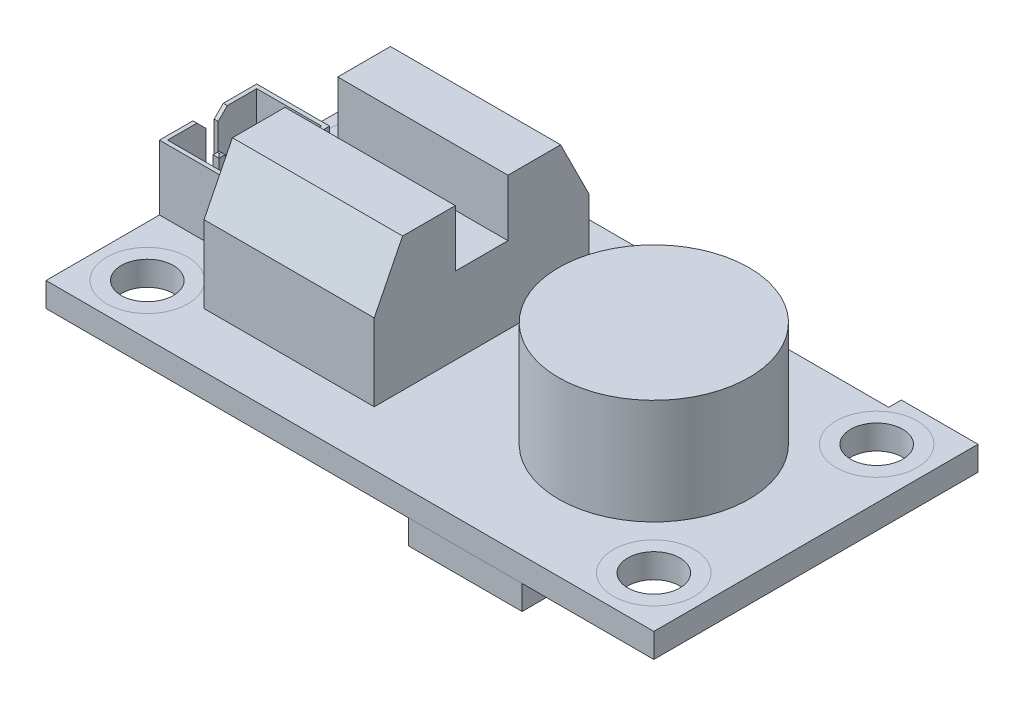
SolidWorks part; units mm, degrees
material "A-Glass Fiber"
ref_plane "Front Plane" through (0, 0, 0) normal (0, 0, 1) x (1, 0, 0)
ref_plane "Top Plane" through (0, 0, 0) normal (0, 1, 0) x (1, 0, 0)
ref_plane "Right Plane" through (0, 0, 0) normal (1, 0, 0) x (0, 0, -1)
sketch "Sketch1" plane through (0, 0, 0) normal (0, 1, 0) x (1, 0, 0)
  line L1 (19.05, -10.16) -> (-19.05, -10.16)
  line L2 (19.05, -10.16) -> (19.05, 10.16)
  line L3 (19.05, 10.16) -> (-19.05, 10.16)
  line L4 (-19.05, -10.16) -> (-19.05, 10.16)
  line L5 (19.05, -10.16) -> (-19.05, 10.16) construction
  line L6 (19.05, 10.16) -> (-19.05, -10.16) construction
  point P0 (0, 0)
  dimension "D1" = 38.1
  dimension "D2" = 20.32
extrude "Boss-Extrude1" add sketch "Sketch1" along normal blind 1.524
hole_wizard "#4 Clearance Hole1" positions "Sketch2" profile "Sketch3" hole size "#4" standard "ANSI Inch" end condition through all
sketch "Sketch2" plane through (0, 1.524, 0) normal (0, 1, 0) x (1, 0, 0)
  line L9 (-15.875, 6.985) -> (15.875, 6.985)
  line L10 (-15.875, 6.985) -> (-15.875, -6.985)
  line L11 (-15.875, -6.985) -> (15.875, -6.985)
  line L12 (15.875, 6.985) -> (15.875, -6.985)
  line L13 (19.05, -10.16) -> (19.05, 10.16) construction
  line L14 (19.05, 10.16) -> (-19.05, 10.16) construction
  line L15 (-19.05, 10.16) -> (-19.05, -10.16) construction
  line L16 (-19.05, -10.16) -> (19.05, -10.16) construction
  point P66 (-15.875, 6.985)
  point P67 (15.875, -6.985)
  point P70 (-15.875, -6.985)
  point P71 (15.875, 6.985)
  dimension "D1" = 3.175
  dimension "D2" = 3.175
  dimension "D3" = 3.175
  dimension "D4" = 3.175
sketch "Sketch3" plane through (-15.875, 1.524, -6.985) normal (1, 0, 0) x (0, 0, 1)
  line L0 (0, 0) -> (0, 1.524)
  line L1 (0, 1.524) -> (1.6319, 1.524)
  line L2 (1.6319, 1.524) -> (1.6319, 0)
  line L5 (1.6319, 0) -> (0, 0)
  line L11 (0, -6.35) -> (0, 107.95) construction
  dimension "Thru Hole Dia." = 3.2639
  dimension "Thru Hole Depth" = 1.524
sketch "Sketch4" plane through (0, 1.524, 0) normal (0, 1, 0) x (1, 0, 0)
  line L0 (-19.05, 10.16) -> (-19.05, -10.16) construction
  line L1 (-19.05, 3.048) -> (-14.478, 3.048)
  line L2 (-19.05, 3.048) -> (-19.05, -3.048)
  line L3 (-19.05, -3.048) -> (-14.478, -3.048)
  line L4 (-14.478, 3.048) -> (-14.478, -3.048)
  point P6 (-14.478, 0)
  dimension "D1" = 6.096
  dimension "D2" = 4.572
extrude "Boss-Extrude2" add sketch "Sketch4" along normal blind 4.064
sketch "Sketch5" plane through (0, 1.524, 0) normal (0, 1, 0) x (1, 0, 0)
  line L0 (19.05, -10.16) -> (19.05, 10.16) construction
  circle A0 centre (8.89, 0) radius 5.969
  dimension "D1" = 10.16
  dimension "D2" = 11.938
extrude "Boss-Extrude3" add sketch "Sketch5" along normal blind 6.604
sketch "Sketch6" plane through (0, 1.524, 0) normal (0, 1, 0) x (1, 0, 0)
  line L1 (-1.905, -6.731) -> (-12.573, -6.731)
  line L2 (-1.905, -6.731) -> (-1.905, 6.731)
  line L3 (-1.905, 6.731) -> (-12.573, 6.731)
  line L4 (-12.573, -6.731) -> (-12.573, 6.731)
  line L5 (-1.905, -6.731) -> (-12.573, 6.731) construction
  line L6 (-1.905, 6.731) -> (-12.573, -6.731) construction
  circle A1 centre (8.89, 0) radius 5.969 construction
  point P0 (-7.239, 0)
  dimension "D1" = 13.462
  dimension "D2" = 10.668
  dimension "D3" = 4.826
extrude "Boss-Extrude4" add sketch "Sketch6" along normal blind 4.826
sketch "Sketch7" plane through (-12.573, 0, 0) normal (-1, 0, 0) x (0, 0, 1)
  line L1 (-6.731, 6.35) -> (-4.953, 9.906)
  line L6 (0, 0) -> (0, 50000) construction
  line L18 (6.731, 6.35) -> (4.953, 9.906)
  line L19 (-4.953, 9.906) -> (-1.651, 9.906)
  line L20 (4.953, 9.906) -> (1.651, 9.906)
  line L21 (-1.651, 9.906) -> (-1.651, 6.35)
  line L22 (-6.731, 6.35) -> (6.731, 6.35) construction
  line L23 (1.651, 9.906) -> (1.651, 6.35)
  line L24 (-6.731, 6.35) -> (-1.651, 6.35)
  line L25 (6.731, 6.35) -> (1.651, 6.35)
  dimension "D1" = 3.556
  dimension "D2" = 3.302
  dimension "D3" = 3.302
extrude "Boss-Extrude5" add sketch "Sketch7" against normal up to surface (10.668 mm away) up to face at (-1.905, 3.937, 0)
sketch "Sketch8" plane through (0, 0, 0) normal (0, -1, 0) x (1, 0, 0)
  line L0 (19.05, -10.16) -> (-19.05, -10.16) construction
  line L1 (3.302, -10.16) -> (11.176, -10.16)
  line L2 (3.302, -10.16) -> (3.302, -4.572)
  line L3 (3.302, -4.572) -> (11.176, -4.572)
  line L4 (11.176, -10.16) -> (11.176, -4.572)
  line L5 (19.05, 10.16) -> (19.05, -10.16) construction
  dimension "D1" = 5.588
  dimension "D2" = 7.874
  dimension "D3" = 7.874
extrude "Boss-Extrude6" add sketch "Sketch8" along normal blind 3.048
sketch "Sketch9" plane through (0, 0, 0) normal (0, -1, 0) x (1, 0, 0)
  line L0 (-19.05, 10.16) -> (19.05, 10.16) construction
  line L1 (3.683, 10.16) -> (10.795, 10.16)
  line L2 (3.683, 10.16) -> (3.683, 5.08)
  line L3 (3.683, 5.08) -> (10.795, 5.08)
  line L4 (10.795, 10.16) -> (10.795, 5.08)
  line L5 (11.176, -4.572) -> (3.302, -4.572) construction
  point P8 (7.239, -4.572)
  point P9 (7.239, 5.08)
  dimension "D1" = 5.08
  dimension "D2" = 7.112
extrude "Boss-Extrude7" add sketch "Sketch9" along normal blind 1.524
sketch "Sketch10" plane through (0, 0, 0) normal (0, -1, 0) x (1, 0, 0)
  line L0 (10.795, 5.08) -> (10.795, 10.16) construction
  line L1 (14.859, 2.032) -> (12.319, 2.032)
  line L2 (14.859, 2.032) -> (14.859, -2.032)
  line L3 (14.859, -2.032) -> (12.319, -2.032)
  line L4 (12.319, 2.032) -> (12.319, -2.032)
  point P4 (14.859, 0)
  dimension "D1" = 4.064
  dimension "D2" = 2.54
  dimension "D3" = 1.524
extrude "Boss-Extrude8" add sketch "Sketch10" along normal blind 1.016
sketch "Sketch11" plane through (0, 0, 0) normal (0, -1, 0) x (1, 0, 0)
  line L0 (3.683, 10.16) -> (3.683, 5.08) construction
  line L1 (1.651, -2.54) -> (6.731, -2.54)
  line L2 (1.651, -2.54) -> (1.651, 2.54)
  line L3 (1.651, 2.54) -> (6.731, 2.54)
  line L4 (6.731, -2.54) -> (6.731, 2.54)
  line L5 (1.651, -2.54) -> (6.731, 2.54) construction
  line L6 (1.651, 2.54) -> (6.731, -2.54) construction
  point P0 (4.191, 0)
  dimension "D1" = 5.08
  dimension "D2" = 2.032
extrude "Boss-Extrude9" add sketch "Sketch11" along normal blind 1.016
sketch "Sketch12" plane through (0, 0, 0) normal (0, -1, 0) x (1, 0, 0)
  line L0 (-19.05, 10.16) -> (3.683, 10.16) construction
  line L1 (-0.381, 6.096) -> (-4.445, 6.096)
  line L2 (-0.381, 6.096) -> (-0.381, 8.128)
  line L3 (-0.381, 8.128) -> (-4.445, 8.128)
  line L4 (-4.445, 6.096) -> (-4.445, 8.128)
  line L5 (-0.381, 6.096) -> (-4.445, 8.128) construction
  line L6 (-0.381, 8.128) -> (-4.445, 6.096) construction
  line L7 (3.683, 10.16) -> (3.683, 5.08) construction
  point P0 (-2.413, 7.112)
  dimension "D1" = 2.032
  dimension "D2" = 4.064
  dimension "D3" = 2.032
  dimension "D4" = 4.064
extrude "Boss-Extrude10" add sketch "Sketch12" along normal blind 1.016
sketch "Sketch13" plane through (0, 0, 0) normal (0, -1, 0) x (1, 0, 0)
  line L0 (3.302, -4.572) -> (3.302, -10.16) construction
  line L1 (-2.286, -7.62) -> (-5.334, -7.62)
  line L2 (-2.286, -7.62) -> (-2.286, -4.572)
  line L3 (-2.286, -4.572) -> (-5.334, -4.572)
  line L4 (-5.334, -7.62) -> (-5.334, -4.572)
  line L5 (-2.286, -7.62) -> (-5.334, -4.572) construction
  line L6 (-2.286, -4.572) -> (-5.334, -7.62) construction
  line L7 (3.302, -10.16) -> (-19.05, -10.16) construction
  point P0 (-3.81, -6.096)
  dimension "D1" = 3.048
  dimension "D2" = 5.588
  dimension "D3" = 2.54
extrude "Boss-Extrude11" add sketch "Sketch13" along normal blind 0.508
sketch "Sketch14" plane through (0, 0, 0) normal (0, -1, 0) x (1, 0, 0)
  line L0 (-19.05, -10.16) -> (-19.05, 10.16) construction
  line L1 (-11.43, -4.572) -> (-8.382, -4.572)
  line L2 (-11.43, -4.572) -> (-11.43, -8.128)
  line L3 (-11.43, -8.128) -> (-8.382, -8.128)
  line L4 (-8.382, -4.572) -> (-8.382, -8.128)
  line L5 (-11.43, -4.572) -> (-8.382, -8.128) construction
  line L6 (-11.43, -8.128) -> (-8.382, -4.572) construction
  line L7 (3.302, -10.16) -> (-19.05, -10.16) construction
  point P0 (-9.906, -6.35)
  dimension "D1" = 3.556
  dimension "D2" = 3.048
  dimension "D3" = 7.62
  dimension "D4" = 2.032
extrude "Boss-Extrude12" add sketch "Sketch14" along normal blind 1.016
sketch "Sketch15" plane through (0, 0, 0) normal (0, -1, 0) x (1, 0, 0)
  line L0 (3.302, -10.16) -> (-19.05, -10.16) construction
  line L1 (-16.51, 3.302) -> (-14.478, 3.302)
  line L2 (-16.51, 3.302) -> (-16.51, -0.762)
  line L3 (-16.51, -0.762) -> (-14.478, -0.762)
  line L4 (-14.478, 3.302) -> (-14.478, -0.762)
  line L5 (-16.51, 3.302) -> (-14.478, -0.762) construction
  line L6 (-16.51, -0.762) -> (-14.478, 3.302) construction
  line L7 (-19.05, -10.16) -> (-19.05, 10.16) construction
  point P0 (-15.494, 1.27)
  dimension "D1" = 4.064
  dimension "D2" = 2.032
  dimension "D3" = 9.398
  dimension "D4" = 2.54
extrude "Boss-Extrude13" add sketch "Sketch15" along normal blind 1.524
sketch "Sketch16" plane through (0, 0, 0) normal (0, -1, 0) x (1, 0, 0)
  line L0 (-19.05, -10.16) -> (-19.05, 10.16) construction
  line L1 (-7.874, -1.524) -> (-10.922, -1.524)
  line L2 (-7.874, -1.524) -> (-7.874, 1.524)
  line L3 (-7.874, 1.524) -> (-10.922, 1.524)
  line L4 (-10.922, -1.524) -> (-10.922, 1.524)
  line L5 (-7.874, -1.524) -> (-10.922, 1.524) construction
  line L6 (-7.874, 1.524) -> (-10.922, -1.524) construction
  point P0 (-9.398, 0)
  point P8 (-19.05, 0)
  dimension "D1" = 3.048
  dimension "D2" = 8.128
extrude "Boss-Extrude14" add sketch "Sketch16" along normal blind 1.016
sketch "Sketch17" plane through (0, 0, 0) normal (0, -1, 0) x (1, 0, 0)
  line L0 (-19.05, -10.16) -> (-19.05, 10.16) construction
  line L1 (3.302, -10.16) -> (-19.05, -10.16) construction
  circle A0 centre (-11.684, -3.556) radius 0.508
  dimension "D1" = 1.016
  dimension "D2" = 6.858
  dimension "D3" = 6.096
extrude "Boss-Extrude15" add sketch "Sketch17" along normal blind 1.524
pattern_linear "LPattern1" count 4 spacing 2.794 along (1, 0, 0) of "Boss-Extrude15"
mirror "Mirror1" about plane through (0, 0, 0) normal (0, 0, 1) of "LPattern1", "Boss-Extrude15"
sketch "Sketch22" plane through (0, 1.524, 0) normal (0, 1, 0) x (1, 0, 0)
  line L0 (19.05, 10.16) -> (-19.05, 10.16) construction
  line L1 (0.635, 10.16) -> (14.2431, 10.16)
  line L2 (0.635, 10.16) -> (0.635, 9.3663)
  line L3 (0.635, 9.3663) -> (14.2431, 9.3663)
  line L4 (14.2431, 10.16) -> (14.2431, 9.3663)
  line L5 (-1.905, 6.731) -> (-1.905, 4.953) construction
  circle A0 centre (15.875, 6.985) radius 1.6319 construction
  dimension "D1" = 0.7937
  dimension "D2" = 2.54
extrude "Cut-Extrude2" cut sketch "Sketch22" against normal up to surface (1.524 mm away) up to face at (-3.302, 0, 4.064)
sketch "Sketch18" plane through (-19.05, 0, 0) normal (-1, 0, 0) x (0, 0, 1)
  line L0 (-3.048, 1.524) -> (3.048, 1.524)
split line "Split Line1"
sketch "Sketch19" plane through (0, 0, 10.16) normal (0, 0, 1) x (1, 0, 0)
  line L0 (3.683, 0) -> (10.795, 0)
  line L1 (11.176, 0) -> (3.302, 0) construction
  line L2 (10.795, 0) -> (19.05, 0) construction
split line "Split Line2"
sketch "Sketch23" plane through (0, 1.524, 0) normal (0, 1, 0) x (1, 0, 0)
  circle A0 centre (-15.875, 6.985) radius 2.54
  circle A1 centre (15.875, 6.985) radius 2.54
  circle A2 centre (15.875, -6.985) radius 2.54
  circle A3 centre (-15.875, -6.985) radius 2.54
  dimension "D1" = 5.08
split line "Split Line3"
sketch "Sketch24" plane through (0, 5.588, 0) normal (0, 1, 0) x (1, 0, 0)
  line L8 (-18.796, 2.794) -> (-18.796, -2.794)
  line L9 (-18.796, -2.794) -> (-14.732, -2.794)
  line L10 (-14.732, -2.794) -> (-14.732, 2.794)
  line L11 (-14.732, 2.794) -> (-18.796, 2.794)
  line L12 (-18.796, 2.794) -> (-18.796, -2.794)
  line L13 (-18.796, -2.794) -> (-14.732, -2.794)
  line L14 (-14.732, -2.794) -> (-14.732, 2.794)
  line L15 (-14.732, 2.794) -> (-18.796, 2.794)
  dimension "D1" = 0.254
extrude "Cut-Extrude3" cut sketch "Sketch24" against normal offset from surface (3.556 mm away) 0.508 contours L12 L13 L14 L15 up to face at (15.875, 1.524, 9.525)
sketch "Sketch25" plane through (0, 2.032, 0) normal (0, 1, 0) x (1, 0, 0)
  line L0 (-17.018, 2.794) -> (-17.018, -2.794) construction
  line L1 (-14.732, 2.794) -> (-18.796, 2.794) construction
  line L2 (-14.732, -2.794) -> (-18.796, -2.794) construction
  line L3 (-18.796, 2.794) -> (-18.796, -2.794) construction
  line L4 (-17.018, 0) -> (-18.796, 0) construction
  line L5 (-16.8275, 1.143) -> (-17.2085, 1.143)
  line L6 (-16.8275, 1.143) -> (-16.8275, 1.524)
  line L7 (-16.8275, 1.524) -> (-17.2085, 1.524)
  line L8 (-17.2085, 1.143) -> (-17.2085, 1.524)
  line L9 (-16.8275, 1.143) -> (-17.2085, 1.524) construction
  line L10 (-16.8275, 1.524) -> (-17.2085, 1.143) construction
  line L11 (-16.8275, -1.524) -> (-17.2085, -1.524)
  line L12 (-16.8275, -1.524) -> (-16.8275, -1.143)
  line L13 (-16.8275, -1.143) -> (-17.2085, -1.143)
  line L14 (-17.2085, -1.524) -> (-17.2085, -1.143)
  line L15 (-16.8275, -1.524) -> (-17.2085, -1.143) construction
  line L16 (-16.8275, -1.143) -> (-17.2085, -1.524) construction
  line L17 (-18.796, -2.794) -> (-18.796, 2.794) construction
  point P8 (-17.018, 1.3335)
  point P13 (-17.018, -1.3335)
  dimension "D1" = 1.778
  dimension "D2" = 0.381
  dimension "D3" = 1.143
  dimension "D4" = 1.143
extrude "Boss-Extrude16" add sketch "Sketch25" along normal offset from surface (3.048 mm away) 0.508 up to face at (-16.764, 5.588, 0)
chamfer "Chamfer1" distance 0.127 angle 45 8 edges at (-16.8275, 5.08, 1.3335) (-17.018, 5.08, 1.524) (-17.2085, 5.08, 1.3335) (-17.018, 5.08, 1.143) (-16.8275, 5.08, -1.3335) (-17.018, 5.08, -1.143) (-17.2085, 5.08, -1.3335) (-17.018, 5.08, -1.524)
sketch "Sketch26" plane through (-19.05, 0, 0) normal (-1, 0, 0) x (0, 0, 1)
  line L0 (0, 5.588) -> (0, 1.524) construction
  line L1 (-3.048, 5.588) -> (3.048, 5.588) construction
  line L2 (-3.048, 1.524) -> (3.048, 1.524) construction
  line L3 (-0.9525, 5.588) -> (-0.381, 5.0165)
  line L4 (0.9525, 5.588) -> (0.381, 5.0165)
  line L5 (-0.381, 5.0165) -> (-0.381, 2.286)
  line L6 (0.381, 5.0165) -> (0.381, 2.286)
  line L7 (-0.381, 2.286) -> (0.381, 2.286)
  line L8 (-0.9525, 5.588) -> (0.9525, 5.588)
  point P12 (0, 2.286)
  dimension "D1" = 0.762
  dimension "D2" = 135
  dimension "D3" = 1.905
  dimension "D4" = 0.762
extrude "Cut-Extrude4" cut sketch "Sketch26" against normal up to surface (0.254 mm away) up to face at (-18.796, 3.81, 0)
chamfer "Chamfer2" distance 1.778 angle 57 2 edges at (3.302, -3.048, -7.366) (11.176, -3.048, -7.366)
